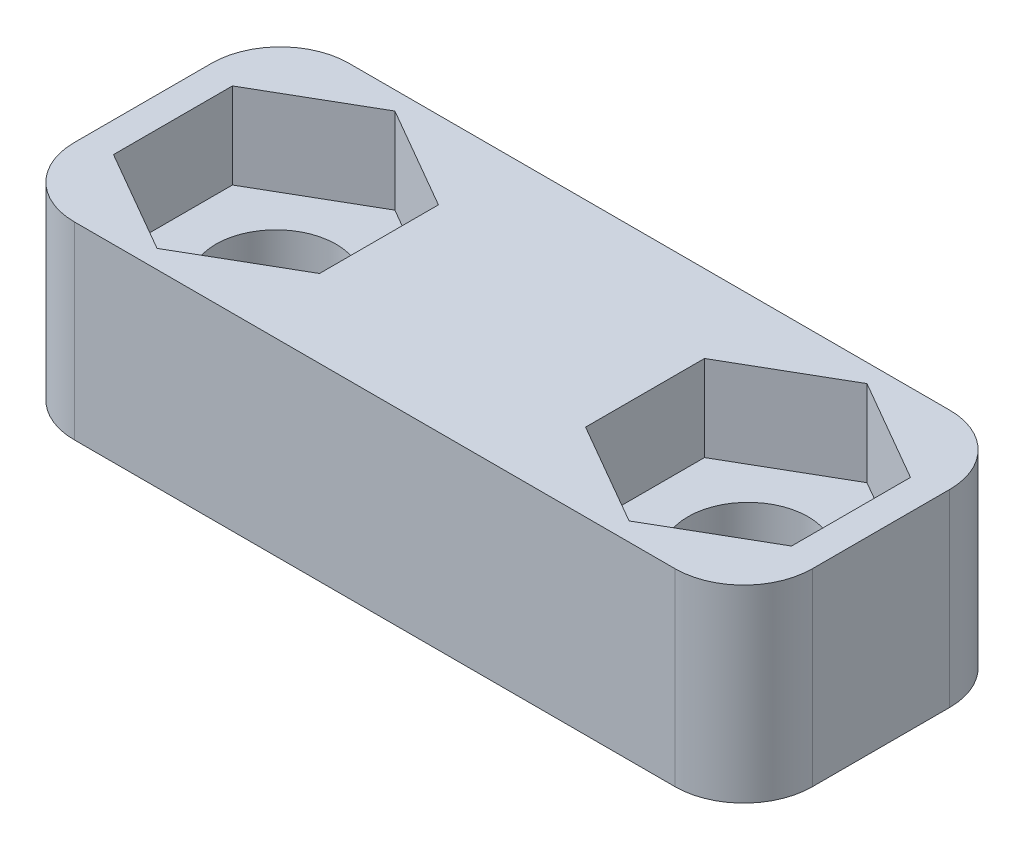
SolidWorks part; units mm, degrees
ref_plane "Front Plane" through (0, 0, 0) normal (0, 0, 1) x (1, 0, 0)
ref_plane "Top Plane" through (0, 0, 0) normal (0, 1, 0) x (1, 0, 0)
ref_plane "Right Plane" through (0, 0, 0) normal (1, 0, 0) x (0, 0, -1)
sketch "Sketch1" plane through (0, 0, 0) normal (0, 0, 1) x (1, 0, 0)
  line L2 (0, 0) -> (0, -5.5)
  line L3 (0, -5.5) -> (21.5, -5.5)
  line L4 (21.5, 0) -> (21.5, -5.5)
  line L8 (0, 0) -> (21.5, 0)
  point P4 (-14.9393, -0.692)
  point P5 (0, 0)
  point P7 (-1.4825, -0.692)
  point P11 (-1.0066, -2.5382)
  point P12 (-5.7728, -2.7258)
  point P13 (-3.9386, -2.516)
  dimension "D1" = 21.5
  dimension "D2" = 5.5
extrude "Boss-Extrude1" add sketch "Sketch1" along normal blind 8
sketch "Sketch2" plane through (0, -5.5, 0) normal (0, -1, 0) x (1, 0, 0)
  line L0 (0, 8) -> (0, 0) construction
  line L1 (0, 8) -> (21.5, 8) construction
  circle A0 centre (3.875, 4) radius 1.75
  circle A1 centre (17.625, 4) radius 1.75
  point P4 (0, 0)
  point P7 (0, 4)
  point P10 (10.75, 8)
  dimension "D1" = 3.5
  dimension "D2" = 13.75
  dimension "D3" = 6.875
extrude "Cut-Extrude1" cut sketch "Sketch2" against normal through all
sketch "Sketch3" plane through (0, 0, 0) normal (0, 1, 0) x (1, 0, 0)
  line L1 (6.875, -5.7321) -> (6.875, -2.2679)
  line L2 (6.875, -2.2679) -> (3.875, -0.5359)
  line L3 (3.875, -0.5359) -> (0.875, -2.2679)
  line L4 (0.875, -2.2679) -> (0.875, -5.7321)
  line L5 (0.875, -5.7321) -> (3.875, -7.4641)
  line L6 (3.875, -7.4641) -> (6.875, -5.7321)
  line L7 (20.625, -2.2679) -> (17.625, -0.5359)
  line L8 (17.625, -0.5359) -> (14.625, -2.2679)
  line L9 (14.625, -2.2679) -> (14.625, -5.7321)
  line L10 (14.625, -5.7321) -> (17.625, -7.4641)
  line L11 (17.625, -7.4641) -> (20.625, -5.7321)
  line L12 (20.625, -5.7321) -> (20.625, -2.2679)
  circle A0 centre (3.875, -4) radius 3 construction
  circle A1 centre (17.625, -4) radius 3 construction
  point P10 (-8.6075, -5.5454)
  point P19 (0.0842, -5.3467)
  point P20 (0, 0)
  dimension "D1" = 6
extrude "Cut-Extrude2" cut sketch "Sketch3" against normal offset from surface (2.5 mm away) 3 up to face at (3.875, -5.5, 2.25)
ref_plane "Plane1" through (0, 0, 1) normal (0, 0, 1) x (1, 0, 0)
ref_plane "Plane2" through (0, 0, 7) normal (0, 0, 1) x (1, 0, 0)
sketch "Sketch4" plane through (0, 0, 1) normal (0, 0, 1) x (1, 0, 0)
  line L0 (7.5, -5.5) -> (14, -5.5)
  line L1 (0, -5.5) -> (21.5, -5.5) construction
  line L2 (14, -5.5) -> (12.5, -6.5)
  line L3 (12.5, -6.5) -> (9, -6.5)
  line L4 (9, -6.5) -> (7.5, -5.5)
  line L5 (21.5, 0) -> (0, 0) construction
  point P6 (10.75, -6.5)
  point P7 (10.75, -5.5)
  point P8 (8.6886, -6.5)
  point P11 (10.75, 0)
  dimension "D1" = 1
  dimension "D2" = 6.5
  dimension "D3" = 3.5
extrude "Boss-Extrude3" add sketch "Sketch4" along normal blind 1
sketch "Sketch5" plane through (0, 0, 7) normal (0, 0, 1) x (1, 0, 0)
  line L0 (7.5, -5.5) -> (9, -6.5)
  line L1 (9, -6.5) -> (12.5, -6.5)
  line L2 (12.5, -6.5) -> (14, -5.5)
  line L3 (14, -5.5) -> (7.5, -5.5)
extrude "Boss-Extrude4" add sketch "Sketch5" against normal blind 1
fillet "Fillet1" radius 2 4 edges at (0, -2.75, 0) (0, -2.75, 8) (21.5, -2.75, 8) (21.5, -2.75, 0)
